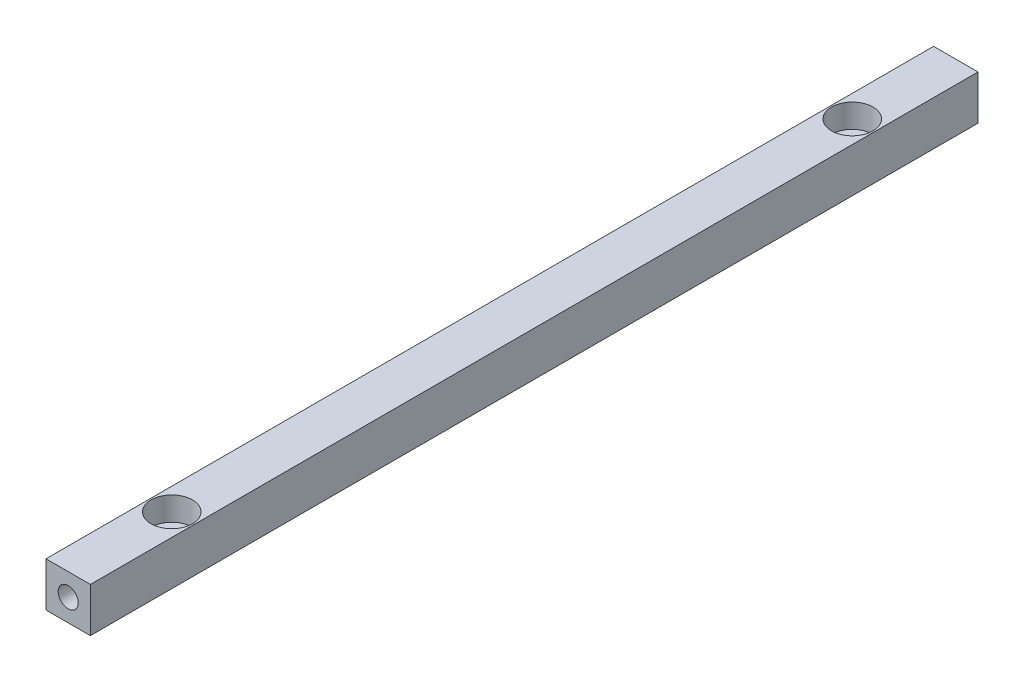
SolidWorks part; units mm, degrees
ref_plane "Front Plane" through (0, 0, 0) normal (0, 0, 1) x (1, 0, 0)
ref_plane "Top Plane" through (0, 0, 0) normal (0, 1, 0) x (1, 0, 0)
ref_plane "Right Plane" through (0, 0, 0) normal (1, 0, 0) x (0, 0, -1)
sketch "Çizim1" plane through (0, 0, 0) normal (0, 0, 1) x (1, 0, 0)
  line L1 (-7.5, 7.5) -> (7.5, 7.5)
  line L2 (-7.5, 7.5) -> (-7.5, -7.5)
  line L3 (-7.5, -7.5) -> (7.5, -7.5)
  line L4 (7.5, 7.5) -> (7.5, -7.5)
  line L5 (-7.5, 7.5) -> (7.5, -7.5) construction
  line L6 (-7.5, -7.5) -> (7.5, 7.5) construction
  point P0 (0, 0)
  dimension "D1" = 15
extrude "Yükseklik-Ekstrüzyon1" add sketch "Çizim1" along normal mid plane 300
hole_wizard "M8 Dişli Delik1" positions "Çizim2" profile "Çizim3" tap size "M8" standard "ISO"
sketch "Çizim2" plane through (0, 0, 150) normal (0, 0, 1) x (1, 0, 0)
  point P0 (0, 0)
sketch "Çizim3" plane through (0, 0, 150) normal (1, 0, 0) x (0, -1, 0)
  line L0 (0, 0) -> (0, 24.2929)
  line L1 (0, 24.2929) -> (3.4, 22.25)
  line L2 (3.4, 22.25) -> (3.4, 0)
  line L5 (3.4, 0) -> (0, 0)
  line L10 (0, 24.2929) -> (-3.4, 22.25) construction
  line L11 (0, -6.35) -> (0, 107.95) construction
  dimension "Tap Drill Dia." = 6.8
  dimension "Tap Drill Depth" = 22.25
  dimension "Drill Angle" = 118
cosmetic thread "Delik Dişi1" parameters "D1"=16, "D2"=8
mirror "Aynalama1" about plane through (0, 0, 0) normal (0, 0, 1) of "M8 Dişli Delik1"
cosmetic thread "Delik Dişi2" parameters "D1"=16, "D2"=8
hole_wizard "Delik1" positions "Çizim4" profile "Çizim5" legacy
sketch "Çizim4" plane through (0, 7.5, 0) normal (0, 1, 0) x (1, 0, 0)
  line L0 (7.5, 150) -> (-7.5, 150) construction
  point P0 (0, 115)
  dimension "D1" = 35
sketch "Çizim5" plane through (0, 7.5, -115) normal (1, 0, 0) x (0, 0, 1)
  line L0 (0, 0) -> (0, 15)
  line L1 (0, 15) -> (4.25, 15)
  line L2 (4.25, 15) -> (4.25, 8)
  line L3 (4.25, 8) -> (7, 8)
  line L4 (7, 8) -> (7, 0)
  line L5 (7, 0) -> (0, 0)
  line L6 (0, 110) -> (0, -10) construction
  dimension "Diameter" = 8.5
  dimension "Depth" = 15
  dimension "C-Bore Diameter" = 14
  dimension "C-Bore Depth" = 8
mirror "Aynalama2" about plane through (0, 0, 0) normal (0, 0, 1) of "Delik1"
